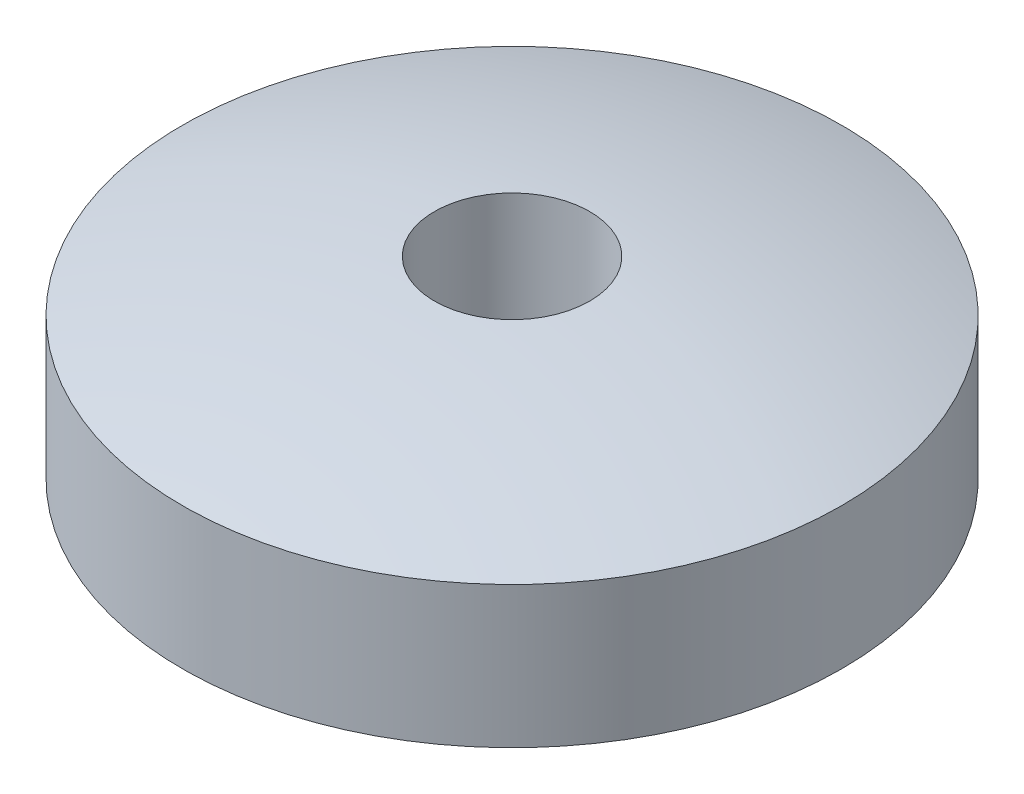
SolidWorks part; units mm, degrees
ref_plane "Alzado" through (0, 0, 0) normal (0, 0, 1) x (1, 0, 0)
ref_plane "Planta" through (0, 0, 0) normal (0, 1, 0) x (1, 0, 0)
ref_plane "Vista lateral" through (0, 0, 0) normal (1, 0, 0) x (0, 0, -1)
sketch "Sketch1" plane through (0, 0, 0) normal (0, 0, 1) x (1, 0, 0)
  line L0 (0, -1000) -> (0, 49000) construction
  line L1 (-1000, 0) -> (49000, 0) construction
  line L2 (-1000.242, 0.193) -> (48999.758, 0.193) construction
  line L3 (-0.106, 0.2629) -> (-0.106, 0.1102)
  line L4 (-0.106, -1000) -> (-0.106, 49000) construction
  line L5 (-0.309, -1000.0539) -> (-0.309, 48999.9461) construction
  line L6 (-0.45, -1000.0608) -> (-0.45, 48999.9392) construction
  line L7 (-0.45, 0.193) -> (-0.45, 0)
  line L8 (-0.45, 0) -> (-0.309, 0)
  arc A0 (-0.106, 0.1102) -> (-0.309, 0) centre (0, -0.3271) ccw
  arc A2 (-0.106, 0.2629) -> (-0.45, 0.193) centre (0, -1.1401) ccw
  dimension "D1" = 0.45
  dimension "D6" = 0.45
  dimension "D5" = 1.407
  dimension "D2" = 0.309
  dimension "D3" = 0.106
  dimension "D4" = 0.193
revolve "Revolve1" add sketch "Sketch1" angle 360 about L0
